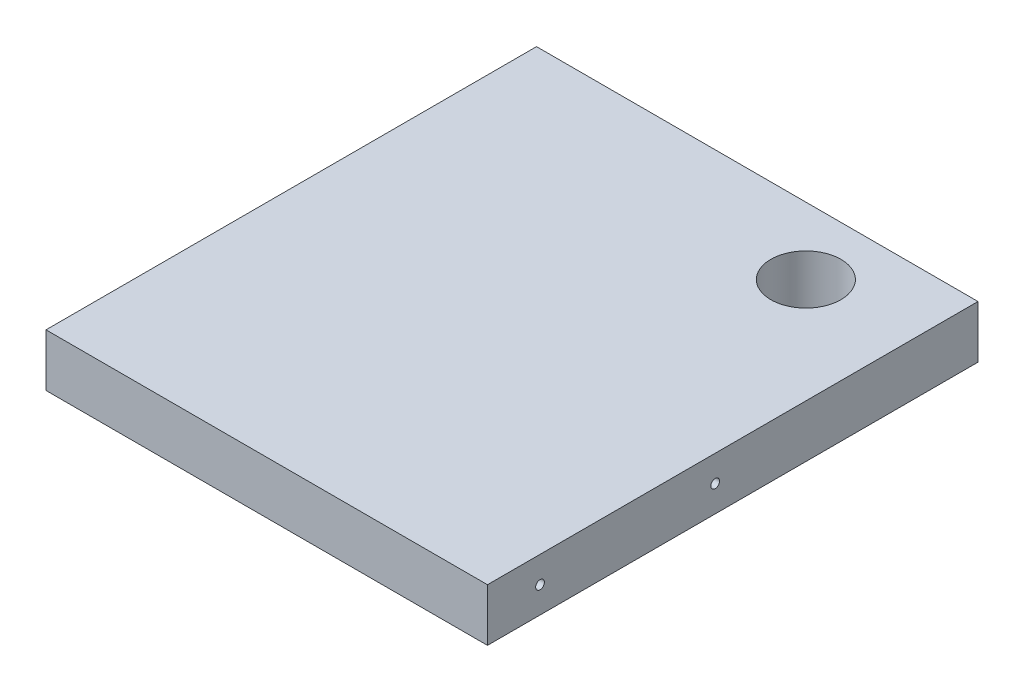
SolidWorks part; units mm, degrees
material "Beech"
ref_plane "Front Plane" through (0, 0, 0) normal (0, 0, 1) x (1, 0, 0)
ref_plane "Top Plane" through (0, 0, 0) normal (0, 1, 0) x (1, 0, 0)
ref_plane "Right Plane" through (0, 0, 0) normal (1, 0, 0) x (0, 0, -1)
sketch "Sketch1" plane through (0, 0, 0) normal (0, 0, 1) x (1, 0, 0)
  line L0 (80.01, 5194.3) -> (80.01, 5232.4) construction
  line L1 (-80.01, 5846.1044) -> (80.01, 5846.1044)
  line L2 (-80.01, 5846.1044) -> (-80.01, 5827.0544)
  line L3 (-80.01, 5827.0544) -> (80.01, 5827.0544)
  line L4 (80.01, 5846.1044) -> (80.01, 5827.0544)
  line L5 (-80.01, 5194.3) -> (-80.01, 5334) construction
  line L6 (-80.01, 5827.0544) -> (-99.06, 5827.0544) construction
  dimension "D1" = 19.05
extrude "Boss-Extrude1" add sketch "Sketch1" along normal offset from surface (177.8 mm away) 101.6
hole_wizard "Hole1" positions "Sketch2" profile "Sketch3" legacy
sketch "Sketch2" plane through (0, 0, -19.05) normal (0, 0, -1) x (-1, 0, 0)
  line L1 (0, 5194.3) -> (0, 5935.98) construction
  line L9 (80.01, 5836.5794) -> (-80.01, 5836.5794) construction
  point P1 (0.1622, 5756.275)
  point P4 (0, 5926.455)
  point P16 (-203.2, 5926.455)
  point P28 (-406.4, 5926.455)
  point P31 (-406.5622, 5756.275)
  point P43 (-203.3622, 5756.275)
  point P55 (-359.618, 5737.225)
  point P61 (-428.6139, 5737.225)
  point P64 (-421.2578, 5578.475)
  point P70 (-319.6578, 5578.475)
  point P82 (-116.4578, 5578.475)
  point P85 (-424.0726, 5559.425)
  point P91 (-358.1042, 5559.425)
  point P94 (-418.2303, 5400.675)
  point P100 (-316.6303, 5400.675)
  point P112 (-113.4303, 5400.675)
  point P115 (-419.5313, 5381.625)
  point P121 (-356.5904, 5381.625)
  point P124 (-415.2028, 5222.875)
  point P130 (-313.6028, 5222.875)
  point P144 (-110.4028, 5222.875)
  point P147 (-414.9901, 5203.825)
  point P153 (-355.0767, 5203.825)
  point P159 (355.0767, 5203.825)
  point P161 (414.9901, 5203.825)
  point P162 (110.4028, 5222.875)
  point P166 (313.6028, 5222.875)
  point P168 (415.2028, 5222.875)
  point P169 (356.5904, 5381.625)
  point P171 (419.5313, 5381.625)
  point P172 (113.4303, 5400.675)
  point P176 (316.6303, 5400.675)
  point P178 (418.2303, 5400.675)
  point P179 (358.1042, 5559.425)
  point P181 (424.0726, 5559.425)
  point P182 (116.4578, 5578.475)
  point P186 (319.6578, 5578.475)
  point P188 (421.2578, 5578.475)
  point P189 (428.6139, 5737.225)
  point P191 (359.618, 5737.225)
  point P195 (203.3622, 5756.275)
  point P199 (406.5622, 5756.275)
  point P200 (406.4, 5926.455)
  point P204 (203.2, 5926.455)
  point P208 (-0.1622, 5756.275)
  point P252 (0, 5836.5794)
  point P254 (-60.96, 5836.5794)
  point P256 (60.96, 5836.5794)
sketch "Sketch3" plane through (-0.1622, 5756.275, -19.05) normal (1, 0, 0) x (0, 1, 0)
  line L0 (0, 0) -> (0, 32.346)
  line L1 (0, 32.346) -> (0.9919, 31.75)
  line L2 (0.9919, 31.75) -> (0.9919, 4.7029)
  line L3 (0.9919, 4.7029) -> (5.08, 0)
  line L4 (5.08, 0) -> (0, 0)
  line L5 (0, -14.3089) -> (0, 102.4216) construction
  line L6 (0, 32.346) -> (-0.9919, 31.75) construction
  line L7 (-0.9919, 4.7029) -> (-5.08, 0) construction
  dimension "Diameter" = 1.9837
  dimension "Depth" = 31.75
  dimension "C-Sink Diameter" = 10.16
  dimension "C-Sink Angle" = 82
  dimension "Drill Angle" = 118
hole_wizard "Hole3" positions "Sketch6" profile "Sketch7" legacy
sketch "Sketch6" plane through (99.06, 0, -2683.51) normal (1, 0, 0) x (0, 0, -1)
  line L0 (-2759.71, 5836.5794) -> (-2861.31, 5836.5794) construction
  point P13 (-2842.26, 5836.5794)
  point P15 (-2778.76, 5836.5794)
sketch "Sketch7" plane through (99.06, 5836.5794, 95.25) normal (0, 1, 0) x (0, 0, -1)
  line L0 (0, 0) -> (0, 32.7039)
  line L1 (0, 32.7039) -> (1.5875, 31.75)
  line L2 (1.5875, 31.75) -> (1.5875, 4.0177)
  line L3 (1.5875, 4.0177) -> (5.08, 0)
  line L4 (5.08, 0) -> (0, 0)
  line L5 (0, -14.3089) -> (0, 102.4216) construction
  line L6 (0, 32.7039) -> (-1.5875, 31.75) construction
  line L7 (-1.5875, 4.0177) -> (-5.08, 0) construction
  dimension "Diameter" = 3.175
  dimension "Depth" = 31.75
  dimension "C-Sink Diameter" = 10.16
  dimension "C-Sink Angle" = 82
  dimension "Drill Angle" = 118
hole_wizard "Hole4" positions "Sketch8" profile "Sketch9" legacy
sketch "Sketch8" plane through (-99.06, 0, -2683.51) normal (-1, 0, 0) x (0, 0, 1)
  line L0 (2759.71, 5836.5794) -> (2861.31, 5836.5794) construction
  point P12 (2842.26, 5836.5794)
  point P14 (2778.76, 5836.5794)
sketch "Sketch9" plane through (-99.06, 5836.5794, 95.25) normal (0, 1, 0) x (0, 0, 1)
  line L0 (0, 0) -> (0, 32.7039)
  line L1 (0, 32.7039) -> (1.5875, 31.75)
  line L2 (1.5875, 31.75) -> (1.5875, 4.0177)
  line L3 (1.5875, 4.0177) -> (5.08, 0)
  line L4 (5.08, 0) -> (0, 0)
  line L5 (0, -14.3089) -> (0, 102.4216) construction
  line L6 (0, 32.7039) -> (-1.5875, 31.75) construction
  line L7 (-1.5875, 4.0177) -> (-5.08, 0) construction
  dimension "Diameter" = 3.175
  dimension "Depth" = 31.75
  dimension "C-Sink Diameter" = 10.16
  dimension "C-Sink Angle" = 82
  dimension "Drill Angle" = 118
hole_wizard "1 (1) Diameter Hole1" positions "Sketch10" profile "Sketch11" hole size "1" standard "ANSI Inch" end condition up to next
sketch "Sketch10" plane through (0, 5827.0544, 0) normal (0, -1, 0) x (-1, 0, 0)
  line L0 (80.01, 0) -> (-80.01, 0) construction
  line L1 (-80.01, -177.8) -> (-80.01, 0) construction
  point P0 (-41.91, -24.2952)
  point P3 (-60.8818, -24.2952)
  dimension "D1" = 24.2952
  dimension "D2" = 38.1
sketch "Sketch11" plane through (41.91, 5827.0544, 24.2952) normal (1, 0, 0) x (0, 0, -1)
  line L0 (0, 0) -> (0, 19.05)
  line L1 (0, 19.05) -> (12.7, 19.05)
  line L2 (12.7, 19.05) -> (12.7, 0)
  line L5 (12.7, 0) -> (0, 0)
  line L11 (0, -6.35) -> (0, 107.95) construction
  dimension "Thru Hole Dia." = 25.4
  dimension "Thru Hole Depth" = 19.05
